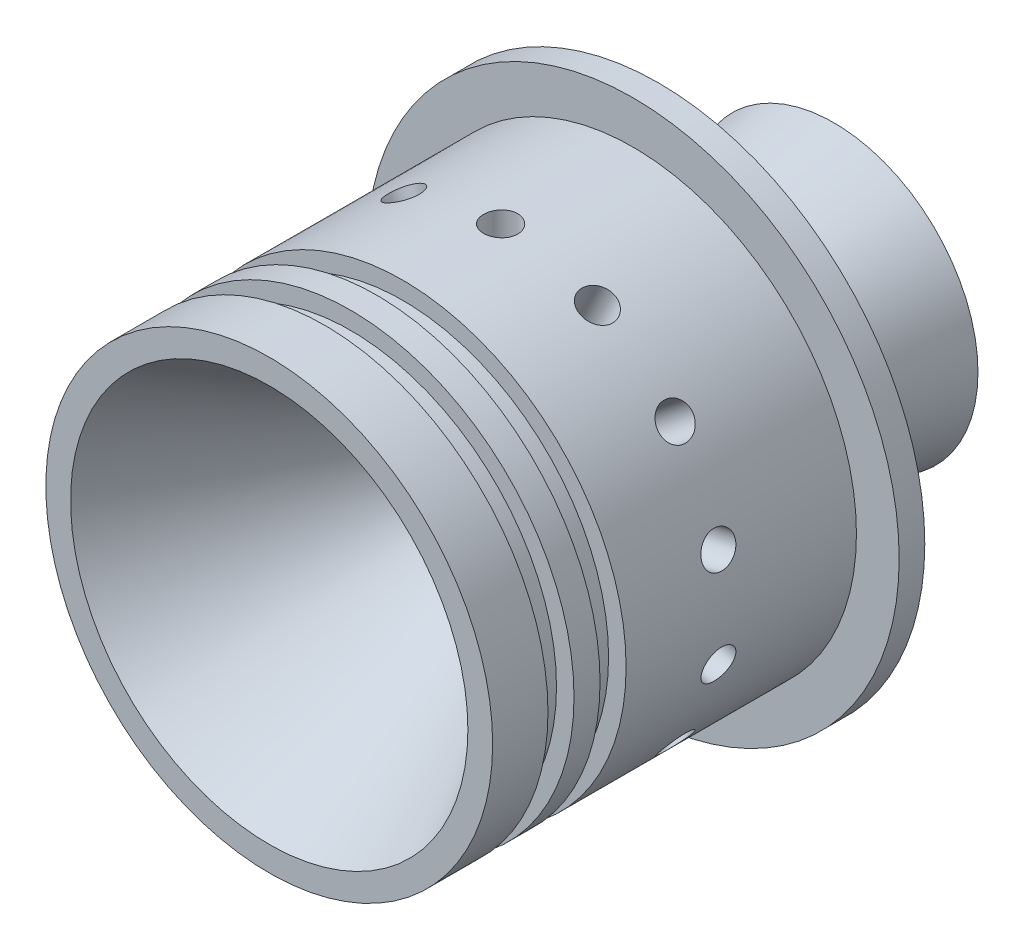
SolidWorks part; units mm, degrees
material "AISI 1045 Steel, cold drawn"
ref_plane "Alzado" through (0, 0, 0) normal (0, 0, 1) x (1, 0, 0)
ref_plane "Planta" through (0, 0, 0) normal (0, 1, 0) x (1, 0, 0)
ref_plane "Vista lateral" through (0, 0, 0) normal (1, 0, 0) x (0, 0, -1)
sketch "Croquis2" plane through (0, 0, 0) normal (1, 0, 0) x (0, 0, -1)
  line L0 (-14.0172, 0) -> (56.1534, 0) construction
  line L1 (0, 23.2509) -> (28.3483, 6.884)
  line L3 (0, 23.2509) -> (0, 26.1493)
  line L4 (0, 26.1493) -> (6.476, 26.1493)
  line L5 (45.5804, 26.0993) -> (45.5804, 12.4942)
  line L7 (66.1004, 16.8559) -> (66.1004, 14.3)
  line L8 (6.476, 26.1493) -> (6.476, 24.0993)
  line L9 (6.476, 24.0993) -> (9.524, 24.0993)
  line L10 (9.524, 24.0993) -> (9.524, 26.1493)
  line L11 (9.524, 26.1493) -> (12.572, 26.1493)
  line L13 (30.786, 6.7937) -> (66.1004, 14.3)
  line L15 (45.5804, 12.4942) -> (66.1004, 16.8559)
  line L16 (28.8483, 6.75) -> (30.3702, 6.75)
  line L18 (16.3437, 13.8149) -> (19.3157, 12.099) construction
  line L19 (19.0363, 6.8) -> (17.4124, 6.8) construction
  line L20 (19.4766, 6.8) -> (20.8834, 6.8) construction
  line L21 (30.5804, 8.6394) -> (30.5804, -5.1694) construction
  line L22 (12.572, 26.1493) -> (12.572, 24.0993)
  line L23 (12.572, 24.0993) -> (15.62, 24.0993)
  line L24 (15.62, 24.0993) -> (15.62, 26.1493)
  line L25 (15.62, 26.1493) -> (42.5804, 26.1493)
  line L26 (45.5804, 26.0993) -> (45.5804, 31.1493)
  line L27 (45.5804, 31.1493) -> (42.5804, 31.1493)
  line L28 (42.5804, 31.1493) -> (42.5804, 26.1493)
  arc A0 (28.8483, 6.75) -> (28.3483, 6.884) centre (28.8483, 7.75) cw
  arc A1 (30.786, 6.7937) -> (30.3702, 6.75) centre (30.3702, 8.75) cw
  point P14 (8, 24.0993)
  point P15 (27.0804, 26.1493)
  point P25 (28.5804, 6.75)
  point P33 (30.5804, 6.75)
  dimension "D18" = 1
  dimension "D19" = 2
  dimension "D2" = 30
  dimension "D4" = 46.5018
  dimension "D5" = 28.6
  dimension "D7" = 52.2986
  dimension "D8" = 8
  dimension "D11" = 18.5
  dimension "D13" = 12
  dimension "D9" = 2.05
  dimension "D10" = 3.048
  dimension "D3" = 13.5
  dimension "D6" = 2
  dimension "D14" = 33.7117
  dimension "D12" = 2.5
  dimension "D15" = 15
  dimension "D16" = 3
  dimension "D17" = 5
revolve "Revolución1" add sketch "Croquis2" angle 360 about L0
ref_plane "Plano1" through (0, 26.1493, 0) normal (0, 1, 0) x (1, 0, 0)
sketch "Croquis3" plane through (0, 26.1493, 0) normal (0, 1, 0) x (1, 0, 0)
  line L0 (26.1493, 45.5804) -> (-26.1493, 45.5804) construction
  point P0 (0, 27.0804)
  dimension "D1" = 18.5
hole_wizard "Ø4.0mm Dowel Hole1" positions "Croquis3" profile "Croquis5" hole size "Ø4.0" standard "ANSI Metric"
sketch "Croquis5" plane through (0, 26.1493, -27.0804) normal (1, 0, 0) x (0, 0, 1)
  line L0 (0, 0) -> (0, 8.2017)
  line L1 (0, 8.2017) -> (2, 7)
  line L2 (2, 7) -> (2, 0)
  line L5 (2, 0) -> (0, 0)
  line L10 (0, 8.2017) -> (-2, 7) construction
  line L11 (0, -6.35) -> (0, 107.95) construction
  dimension "Hole Dia." = 4
  dimension "Hole Depth" = 7
  dimension "Drill Angle" = 118
pattern_circular "MatrizC1" count 14 over 360 about axis through (0, 0, -15.62) along (0, 0, 1) of "Ø4.0mm Dowel Hole1"
equation "\"Dexit\"=28.6"
equation "\"D5@Croquis2\"=\"Dexit\""
equation "\"IDCase\"= 52.5018"
equation "\"D7@Croquis2\"=\"IDCaseReal\""
equation "\"RadialClearance\"= 0.004in"
equation "\"IDCaseReal\"= \"IDCase\" - \"RadialClearance\" * 2"
equation "\"OringXlocation\"=8"
equation "\"D8@Croquis2\"=\"OringXlocation\""
equation "\"G\"= 3.05mm'O-ring widht gland 0.12<G<0.125 in"
equation "\"D\"= 2.03mm'O-ring depth gland 0.08<D<0.084 in"
equation "\"ScrewXlocation\"= 15 + 3.5'Location plus radius screw M7"
equation "\"D11@Croquis2\"=\"ScrewXlocation\""
equation "\"NozzleBellThickness\"=2.5"
equation "\"D1@Croquis3\"=\"ScrewXlocation\""
equation "\"DnozzleThroat\"=13.5"
equation "\"LengthNozzleThroat\"=2"
equation "\"OuterNozzleBellThickness\"=2"
equation "\"DivergenceAngle\"=12"
equation "\"D13@Croquis2\"=\"DivergenceAngle\""
equation "\"ConvergenceAngle\"=30"
equation "\"D2@Croquis2\"=\"ConvergenceAngle\""
equation "\"ConvergenceThroatRadius\"= 3"
equation "\"DivergenceThroatRadius\"=5"
equation "\"Dchamber\"= \"IDCase\" - 2 * \"AblativeThickness\""
equation "\"D4@Croquis2\"=\"Dchamber\""
equation "\"AblativeThickness\"= 3mm"
equation "\"D3@Croquis2\"=\"DnozzleThroat\""
equation "\"D6@Croquis2\"=\"LengthNozzleThroat\""
equation "\"D12@Croquis2\"=\"NozzleBellThickness\""
